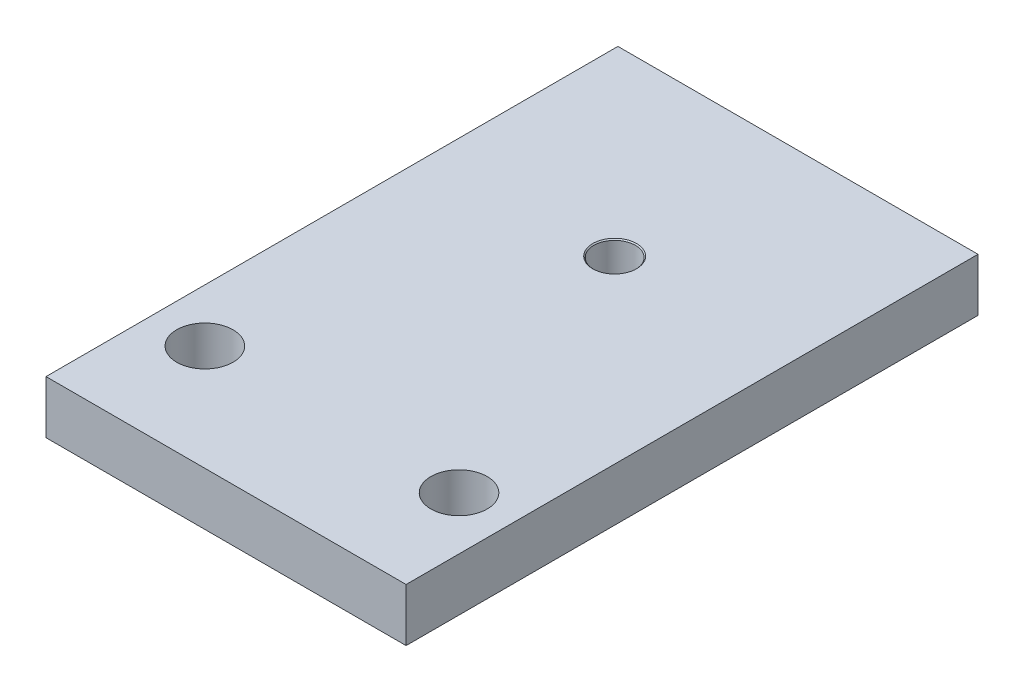
SolidWorks part; units mm, degrees
ref_plane "Front Plane" through (0, 0, 0) normal (0, 0, 1) x (1, 0, 0)
ref_plane "Top Plane" through (0, 0, 0) normal (0, 1, 0) x (1, 0, 0)
ref_plane "Right Plane" through (0, 0, 0) normal (1, 0, 0) x (0, 0, -1)
sketch "Sketch1" plane through (0, 0, 0) normal (0, 1, 0) x (1, 0, 0)
  line L1 (21.59, -34.29) -> (-21.59, -34.29)
  line L2 (21.59, -34.29) -> (21.59, 34.29)
  line L3 (21.59, 34.29) -> (-21.59, 34.29)
  line L4 (-21.59, -34.29) -> (-21.59, 34.29)
  line L5 (21.59, -34.29) -> (-21.59, 34.29) construction
  line L6 (21.59, 34.29) -> (-21.59, -34.29) construction
  point P0 (0, 0)
  dimension "D1" = 68.58
  dimension "D2" = 43.18
extrude "Boss-Extrude1" add sketch "Sketch1" along normal blind 6.35
ref_plane "Plane1" through (28.7045, 9.2463, 34.29) normal (-1, 0, 0) x (0, 0, 1)
sketch "Sketch3" plane through (0, 0, 0) normal (0, -1, 0) x (1, 0, 0)
  line L0 (66.4507, 8.89) -> (-1152.7493, 8.89) construction
  line L1 (66.4507, 34.29) -> (-1152.7493, 34.29) construction
  line L2 (66.4507, 8.89) -> (-1152.7493, 8.89)
  line L3 (66.4507, 34.29) -> (-1152.7493, 34.29)
hole_wizard "1/4 Clearance Hole1" positions "Sketch4" profile "Sketch5" hole size "1/4" standard "ANSI Inch" end condition through all
sketch "Sketch4" plane through (0, 6.35, 0) normal (0, 1, 0) x (1, 0, 0)
  line L0 (-21.59, -8.89) -> (-21.59, -34.29) construction
  line L1 (66.4507, -8.89) -> (-1152.7493, -8.89) construction
  line L2 (-21.59, 34.29) -> (-21.59, -34.29) construction
  line L4 (-21.59, -21.59) -> (21.59, -21.59) construction
  line L5 (21.59, -34.29) -> (21.59, 34.29) construction
  point P15 (-15.24, -21.59)
  point P17 (15.24, -21.59)
  point P20 (0, -21.59)
  dimension "D1" = 15.24
  dimension "D2" = 15.24
sketch "Sketch5" plane through (15.24, 6.35, 21.59) normal (1, 0, 0) x (0, 0, 1)
  line L0 (0, 0) -> (0, 6.35)
  line L1 (0, 6.35) -> (3.3782, 6.35)
  line L2 (3.3782, 6.35) -> (3.3782, 0)
  line L5 (3.3782, 0) -> (0, 0)
  line L11 (0, -6.35) -> (0, 107.95) construction
  dimension "Thru Hole Dia." = 6.7564
  dimension "Thru Hole Depth" = 6.35
sketch "Sketch6" plane through (0, 0, 0) normal (0, -1, 0) x (1, 0, 0)
  circle A0 centre (0, -12.31) radius 10.985 construction
  circle A1 centre (15.5, 3.19) radius 2.155 construction
  circle A2 centre (-15.5, 3.19) radius 2.155 construction
  circle A3 centre (-15.5, -27.81) radius 2.155 construction
  circle A4 centre (15.5, -27.81) radius 2.155 construction
  circle A5 centre (0, -12.31) radius 10.985
  circle A6 centre (15.5, 3.19) radius 2.155
  circle A7 centre (-15.5, 3.19) radius 2.155
  circle A8 centre (-15.5, -27.81) radius 2.155
  circle A9 centre (15.5, -27.81) radius 2.155
sketch "Sketch7" plane through (0, 0, 0) normal (0, -1, 0) x (1, 0, 0)
  circle A0 centre (0, -12.31) radius 2.5
  dimension "D1" = 5
extrude "Cut-Extrude1" cut sketch "Sketch7" against normal through all
chamfer "Chamfer1" distance 0.127 angle 45 2 edges at (0, 0, -14.81) (0, 6.35, -14.81)
